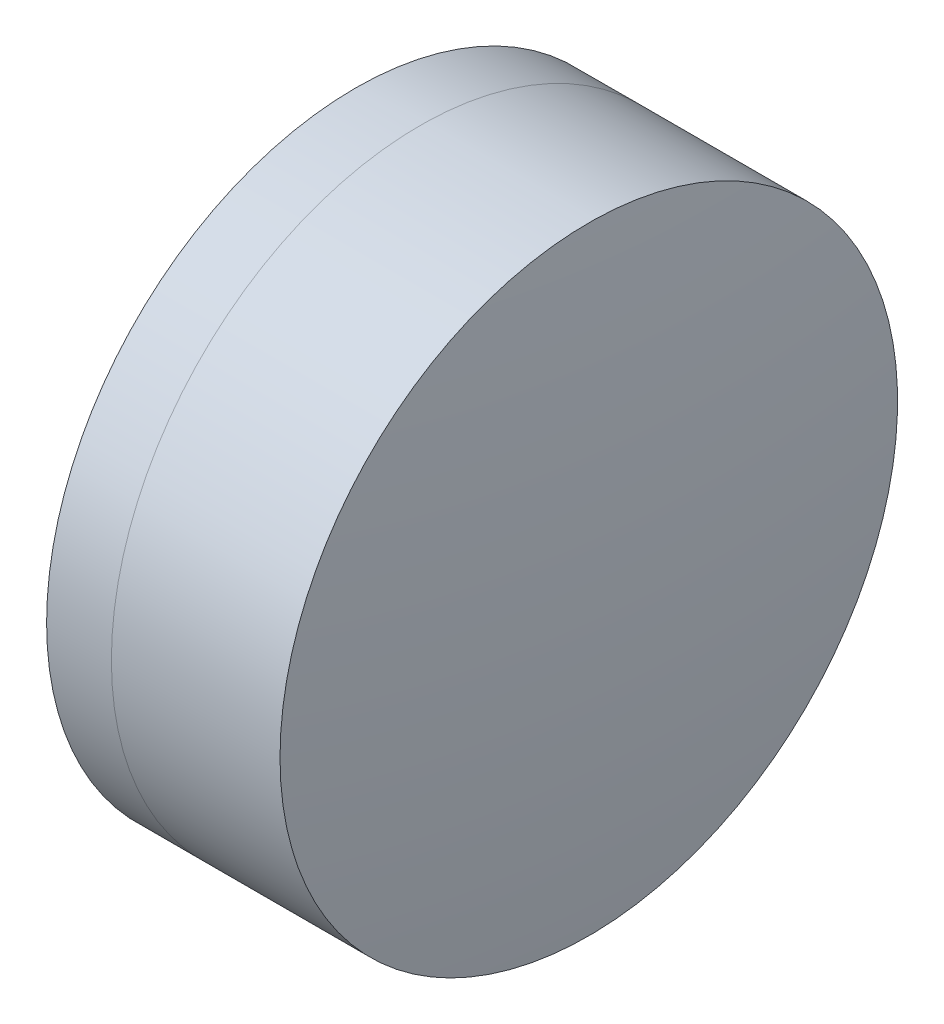
SolidWorks part; units mm, degrees
ref_plane "前视基准面" through (0, 0, 0) normal (0, 0, 1) x (1, 0, 0)
ref_plane "上视基准面" through (0, 0, 0) normal (0, 1, 0) x (1, 0, 0)
ref_plane "右视基准面" through (0, 0, 0) normal (1, 0, 0) x (0, 0, -1)
sketch "草图1" plane through (0, 0, 0) normal (0, 1, 0) x (1, 0, 0)
  line L0 (-9.7026, 0) -> (11.7646, 0) construction
  line L1 (0.8166, -4) -> (1.6558, -4)
  line L2 (0.8166, 4) -> (1.6558, 4)
  arc A0 (1.6558, -4) -> (1.6558, 4) centre (-6.6292, 0) ccw
  arc A1 (0.8166, 4) -> (0.8166, -4) centre (11.1708, 0) ccw
  point P10 (0.0708, 0)
  point P11 (2.5708, 0)
  dimension "D3" = 11.1
  dimension "D4" = 9.2
  dimension "D1" = 4
  dimension "D2" = 4
  dimension "D5" = 2.5
revolve "旋转1" add sketch "草图1" angle 360 about L0
sketch "草图2" plane through (0, 0, 0) normal (0, 1, 0) x (1, 0, 0)
  line L0 (-0.5519, 0) -> (13.3053, 0) construction
  line L2 (1.6558, 4) -> (3.8402, 4)
  line L3 (1.6558, -4) -> (3.8402, -4)
  arc A0 (3.8402, -4) -> (3.8402, 4) centre (-30.7292, 0) ccw
  arc A1 (1.6558, -4) -> (1.6558, 4) centre (-6.6292, 0) ccw construction
  arc A2 (1.6558, -4) -> (1.6558, 4) centre (-6.6292, 0) ccw
  point P4 (2.5708, 0)
  point P8 (4.0708, 0)
  dimension "D1" = 34.8
  dimension "D2" = 1.5
revolve "旋转3" add sketch "草图2" angle 360 about L0
